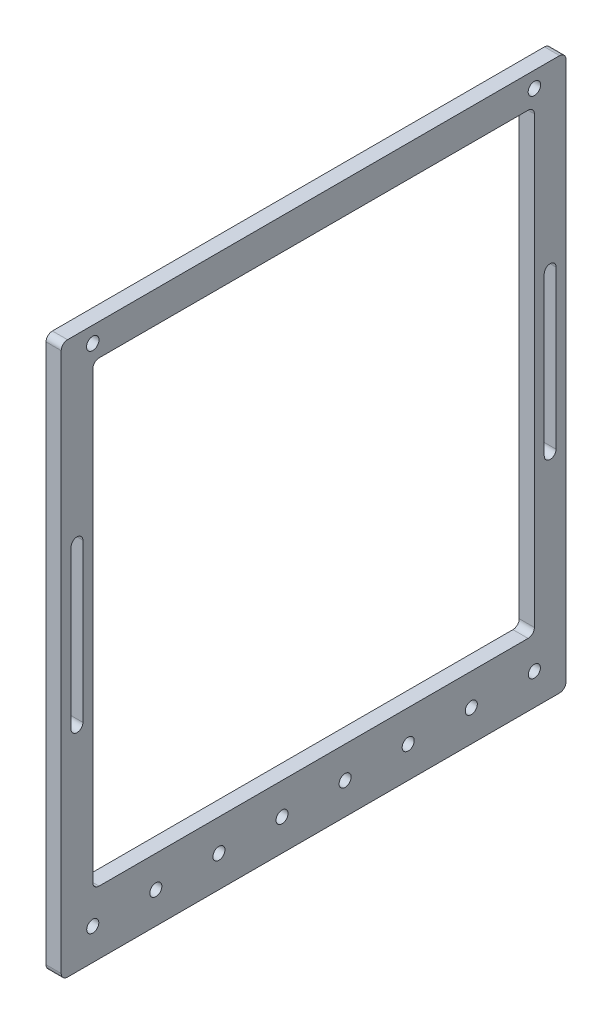
SolidWorks part; units mm, degrees
ref_plane "Front Plane" through (0, 0, 0) normal (0, 0, 1) x (1, 0, 0)
ref_plane "Top Plane" through (0, 0, 0) normal (0, 1, 0) x (1, 0, 0)
ref_plane "Right Plane" through (0, 0, 0) normal (1, 0, 0) x (0, 0, -1)
sketch "Sketch1" plane through (0, 0, 0) normal (1, 0, 0) x (0, 0, -1)
  line L1 (0, 0) -> (177.8, 0)
  line L2 (0, 0) -> (0, -184.15)
  line L3 (0, -184.15) -> (177.8, -184.15)
  line L4 (177.8, 0) -> (177.8, -184.15)
  line L5 (-12.7, 12.7) -> (190.5, 12.7)
  line L6 (-12.7, 12.7) -> (-12.7, -209.55)
  line L7 (-12.7, -209.55) -> (190.5, -209.55)
  line L8 (190.5, 12.7) -> (190.5, -209.55)
  circle A1 centre (0, -196.85) radius 2.425
  circle A2 centre (25.4, -196.85) radius 2.425
  circle A3 centre (50.8, -196.85) radius 2.425
  circle A4 centre (76.2, -196.85) radius 2.425
  circle A5 centre (101.6, -196.85) radius 2.425
  circle A6 centre (127, -196.85) radius 2.425
  circle A7 centre (152.4, -196.85) radius 2.425
  circle A8 centre (177.8, -196.85) radius 2.425
  dimension "D7" = 8
  dimension "D8" = 4.85
  dimension "D9" = 12.7
  dimension "D1" = 184.15
  dimension "D2" = 177.8
  dimension "D3" = 12.7
  dimension "D4" = 12.7
  dimension "D5" = 12.7
  dimension "D6" = 25.4
  dimension "D10" = 12.7
extrude "Boss-Extrude1" add sketch "Sketch1" along normal blind 6.096
fillet "Fillet1" radius 2.54 8 edges at (3.048, 12.7, -190.5) (3.048, 12.7, 12.7) (3.048, -209.55, -190.5) (3.048, -209.55, 12.7) (3.048, -184.15, 0) (3.048, -184.15, -177.8) (3.048, 0, -177.8) (3.048, 0, 0)
sketch "Sketch2" plane through (6.096, 0, 0) normal (1, 0, 0) x (0, 0, -1)
  line L0 (-6.35, -60.325) -> (-6.35, -123.825) construction
  line L1 (-3.9687, -60.325) -> (-3.9687, -123.825)
  line L2 (-8.7313, -60.325) -> (-8.7313, -123.825)
  line L6 (0, -2.54) -> (0, -181.61) construction
  line L7 (0, -92.075) -> (-12.7, -92.075) construction
  line L8 (-12.7, 10.16) -> (-12.7, -207.01) construction
  line L9 (88.9, 0) -> (88.9, -184.15) construction
  line L10 (175.26, 0) -> (2.54, 0) construction
  line L11 (2.54, -184.15) -> (175.26, -184.15) construction
  line L12 (184.15, -60.325) -> (184.15, -123.825) construction
  line L13 (181.7687, -60.325) -> (181.7687, -123.825)
  line L14 (186.5313, -60.325) -> (186.5313, -123.825)
  arc A0 (-3.9687, -60.325) -> (-8.7313, -60.325) centre (-6.35, -60.325) ccw
  arc A1 (-8.7313, -123.825) -> (-3.9687, -123.825) centre (-6.35, -123.825) ccw
  arc A4 (181.7687, -60.325) -> (186.5313, -60.325) centre (184.15, -60.325) cw
  arc A5 (186.5313, -123.825) -> (181.7687, -123.825) centre (184.15, -123.825) cw
  point P2 (-6.35, -92.075)
  point P14 (0, -92.075)
  point P31 (184.15, -92.075)
  dimension "1/16" = 2.3813
  dimension "D2" = 63.5
extrude "Cut-Extrude1" cut sketch "Sketch2" against normal through all
sketch "Sketch3" plane through (6.096, 0, 0) normal (1, 0, 0) x (0, 0, -1)
  line L0 (190.5, -207.01) -> (190.5, 10.16) construction
  line L1 (2.54, -184.15) -> (175.26, -184.15) construction
  line L2 (88.9, 12.7) -> (88.9, -209.55) construction
  line L3 (187.96, 12.7) -> (-10.16, 12.7) construction
  line L4 (-10.16, -209.55) -> (187.96, -209.55) construction
  circle A0 centre (177.8, 6.35) radius 2.505
  circle A1 centre (0, 6.35) radius 2.505
  dimension "D1" = 5.01
  dimension "D2" = 12.7
  dimension "D3" = 190.5
extrude "Cut-Extrude2" cut sketch "Sketch3" against normal through all both and the other way through all
